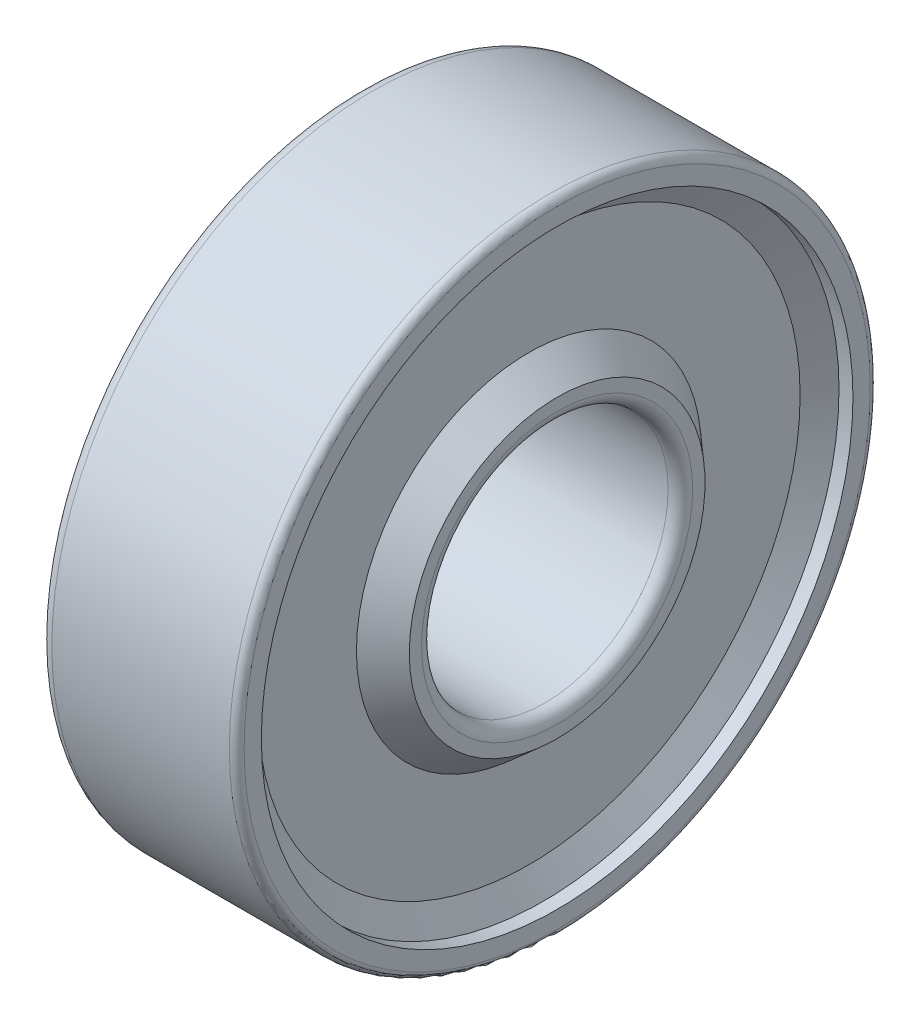
SolidWorks part; units mm, degrees
material "AISI 1020"
ref_plane "Спереди" through (0, 0, 0) normal (0, 0, 1) x (1, 0, 0)
ref_plane "Сверху" through (0, 0, 0) normal (0, 1, 0) x (1, 0, 0)
ref_plane "Справа" through (0, 0, 0) normal (1, 0, 0) x (0, 0, -1)
sketch "Эскиз1" plane through (0, 0, 0) normal (0, 0, 1) x (1, 0, 0)
  line L0 (-1000, 0) -> (49000, 0) construction
  line L1 (0, 5) -> (0, 7) construction
  line L2 (-3.5, 13) -> (3.7, 13)
  line L3 (-4, 12.5) -> (-4, 12)
  line L4 (-3.5, 5) -> (3.5, 5)
  line L5 (4, 12.7) -> (4, 12)
  line L6 (0, 7) -> (0, 9) construction
  line L7 (0, 9) -> (0, 11) construction
  line L8 (0, 11) -> (0, 13) construction
  line L9 (-4, 12) -> (-2.8571, 11)
  line L10 (-2.8571, 11) -> (-2.8571, 7)
  line L11 (-2.8571, 7) -> (-4, 6)
  line L12 (-4, 6) -> (-4, 5.5)
  line L13 (4, 12) -> (3.4345, 12)
  line L14 (3.4345, 12) -> (2.8571, 11)
  line L15 (2.8571, 11) -> (2.8571, 7)
  line L16 (2.8571, 7) -> (4, 6)
  line L17 (4, 6) -> (4, 5.5)
  arc A0 (-3.5, 13) -> (-4, 12.5) centre (-3.5, 12.5) ccw
  arc A1 (-4, 5.5) -> (-3.5, 5) centre (-3.5, 5.5) ccw
  arc A2 (3.5, 5) -> (4, 5.5) centre (3.5, 5.5) ccw
  arc A3 (3.7, 13) -> (4, 12.7) centre (3.7, 12.7) cw
  point P7 (0, 5)
  point P24 (0, 12)
  point P26 (0, 6)
  dimension "_r_" = 0.5
  dimension "_r1_" = 0.3
  dimension "_d_" = 10
  dimension "_D" = 26
  dimension "_T" = 8
  dimension "D2" = 1.1429
  dimension "D3" = 120
revolve "Повернуть1" add sketch "Эскиз1" angle 360 about L0
equation "\"D2@Эскиз1\"=\"_T@Эскиз1\"/7"
